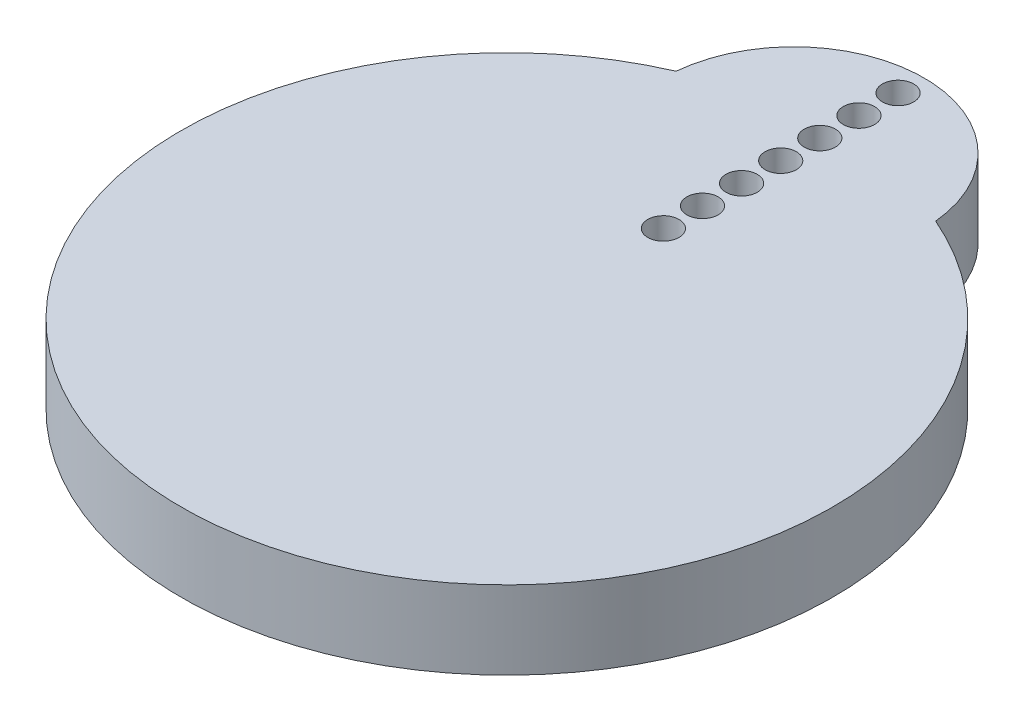
SolidWorks part; units mm, degrees
ref_plane "Front Plane" through (0, 0, 0) normal (0, 0, 1) x (1, 0, 0)
ref_plane "Top Plane" through (0, 0, 0) normal (0, 1, 0) x (1, 0, 0)
ref_plane "Right Plane" through (0, 0, 0) normal (1, 0, 0) x (0, 0, -1)
sketch "Sketch1" plane through (0, 0, 0) normal (0, 1, 0) x (1, 0, 0)
  circle A0 centre (0, 0) radius 12.5
  dimension "D1" = 25
extrude "Boss-Extrude1" add sketch "Sketch1" along normal blind 3
sketch "Sketch3" plane through (0, 3, 0) normal (0, 1, 0) x (1, 0, 0)
  line L0 (0, 0) -> (0, 11)
  line L1 (0, 0) -> (-12.5, 0)
  line L2 (-12.5, 0) -> (12.5, 0)
  line L5 (-5, 11) -> (-12.5, 0)
  line L6 (12.5, 0) -> (5, 11)
  circle A0 centre (0, 0) radius 12.5 construction
  circle A1 centre (0, 11) radius 5
  dimension "D1" = 10
  dimension "D2" = 11
extrude "Boss-Extrude2" add sketch "Sketch3" against normal up to surface (3 mm away) up to face at (0, 0, 12.5)
sketch "Sketch4" plane through (0, 3, 0) normal (0, 1, 0) x (1, 0, 0)
  line L0 (0, 16) -> (0, 0)
  arc A0 (4.9782, 11.4659) -> (-4.9782, 11.4659) centre (0, 11) ccw construction
  circle A1 centre (0, 15) radius 0.6
  circle A2 centre (0, 13.5) radius 0.6
  circle A3 centre (0, 12) radius 0.6
  circle A4 centre (0, 10.5) radius 0.6
  circle A5 centre (0, 9) radius 0.6
  circle A6 centre (0, 7.5) radius 0.6
  circle A7 centre (0, 6) radius 0.6
  dimension "D1" = 1.2
  dimension "D2" = 1
  dimension "D3" = 7
extrude "Cut-Extrude1" cut sketch "Sketch4" against normal blind 10 contours L0 A7 | L0 A7 | L0 A6 | L0 A6 | L0 A5 | L0 A5 | L0 A4 | L0 A4 | L0 A3 | L0 A3 | L0 A2 | L0 A2 | L0 A1 | L0 A1
